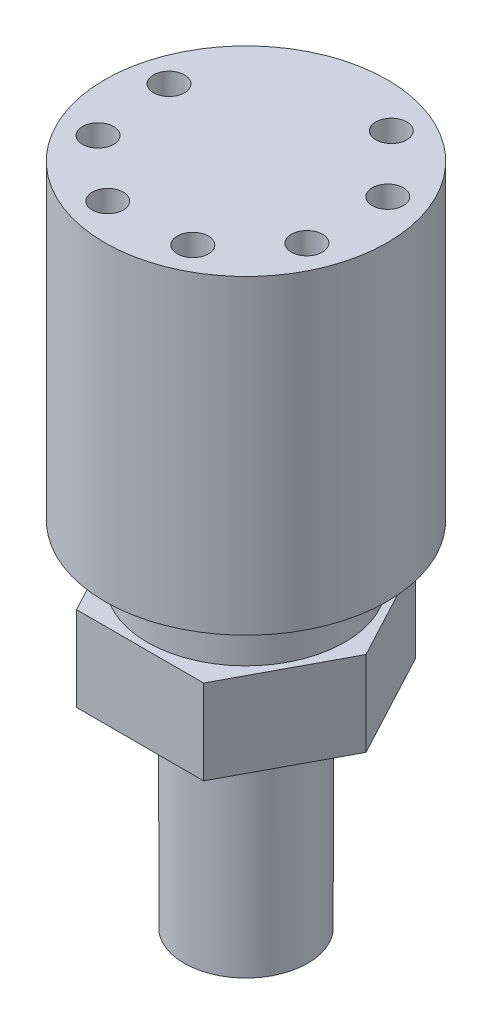
SolidWorks part; units mm, degrees
ref_plane "Front Plane" through (0, 0, 0) normal (0, 0, 1) x (1, 0, 0)
ref_plane "Top Plane" through (0, 0, 0) normal (0, 1, 0) x (1, 0, 0)
ref_plane "Right Plane" through (0, 0, 0) normal (1, 0, 0) x (0, 0, -1)
sketch "Sketch1" plane through (0, 0, 0) normal (0, 1, 0) x (1, 0, 0)
  circle A0 centre (0, 0) radius 8.89
  dimension "D1" = 17.78
extrude "Boss-Extrude1" add sketch "Sketch1" along normal blind 5.08
sketch "Sketch2" plane through (0, 0, 0) normal (0, -1, 0) x (1, 0, 0)
  line L0 (-5.715, 9.525) -> (5.715, 9.525)
  line L1 (5.715, 9.525) -> (10.795, 0)
  line L2 (10.795, 0) -> (5.715, -9.525)
  line L3 (5.715, -9.525) -> (-5.715, -9.525)
  line L4 (-5.715, -9.525) -> (-10.795, 0)
  line L5 (-10.795, 0) -> (-5.715, 9.525)
  line L6 (-10.795, 0) -> (10.795, 0) construction
  circle A0 centre (0, 0) radius 9.525
  point P4 (0, 0)
  dimension "D1" = 19.05
  dimension "D2" = 21.59
extrude "Boss-Extrude2" add sketch "Sketch2" along normal blind 7.62 contours L1 L2 L3 L4 L5 L0
sketch "Sketch3" plane through (0, -7.62, 0) normal (0, -1, 0) x (-1, 0, 0)
  circle A0 centre (0, 0) radius 5.5562
  dimension "D1" = 11.1125
extrude "Boss-Extrude3" add sketch "Sketch3" along normal blind 19.05
cosmetic thread "Cosmetic Thread1" parameters "D2"=9.6012
sketch "Sketch4" plane through (0, 5.08, 0) normal (0, 1, 0) x (1, 0, 0)
  circle A0 centre (0, 0) radius 12.7
  dimension "D1" = 25.4
extrude "Boss-Extrude4" add sketch "Sketch4" along normal blind 27.94
sketch "Sketch5" plane through (0, 33.02, 0) normal (0, 1, 0) x (1, 0, 0)
  circle A0 centre (4.1713, 8.8975) radius 1.397
  circle A1 centre (9.1399, 3.6093) radius 1.397
  circle A2 centre (9.125, -3.6469) radius 1.397
  circle A3 centre (4.1346, -8.9146) radius 1.397
  circle A4 centre (-3.1101, -9.3216) radius 1.397
  circle A5 centre (-8.6591, -4.646) radius 1.397
  circle A6 centre (-9.4867, 2.5629) radius 1.397
  point P16 (0, 0)
  dimension "D1" = 2.794
  dimension "D2" = 7
extrude "Cut-Extrude1" cut sketch "Sketch5" against normal blind 20.32
